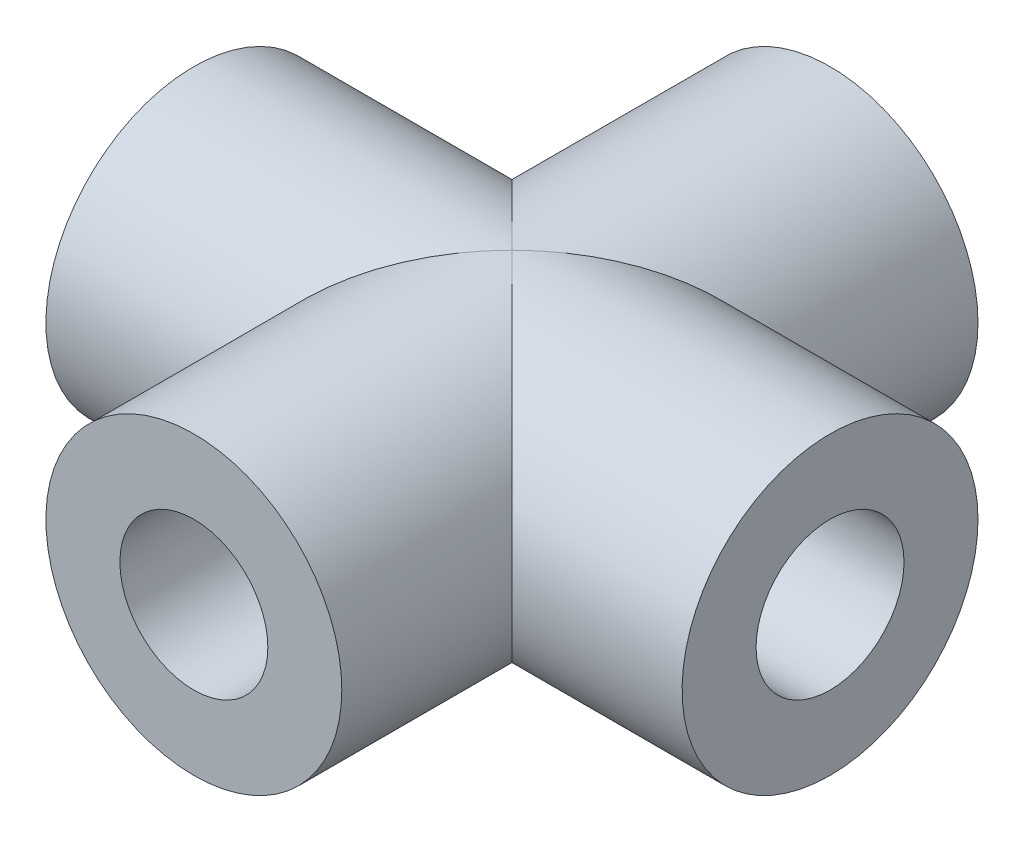
SolidWorks part; units mm, degrees
ref_plane "Front Plane" through (0, 0, 0) normal (0, 0, 1) x (1, 0, 0)
ref_plane "Top Plane" through (0, 0, 0) normal (0, 1, 0) x (1, 0, 0)
ref_plane "Right Plane" through (0, 0, 0) normal (1, 0, 0) x (0, 0, -1)
sketch "Sketch3" plane through (0, 0, 0) normal (0, 0, 1) x (1, 0, 0)
  circle A0 centre (0, 0) radius 6.35
  circle A1 centre (0, 0) radius 12.7
  dimension "D1" = 12.7
  dimension "D2" = 25.4
extrude "Boss-Extrude1" add sketch "Sketch3" along normal mid plane 54.61
sketch "Sketch4" plane through (0, 0, 0) normal (1, 0, 0) x (0, 0, -1)
  circle A0 centre (0, 0) radius 6.35
  circle A1 centre (0, 0) radius 12.7
  dimension "D1" = 12.7
  dimension "D2" = 25.4
extrude "Boss-Extrude2" add sketch "Sketch4" along normal mid plane 54.61
